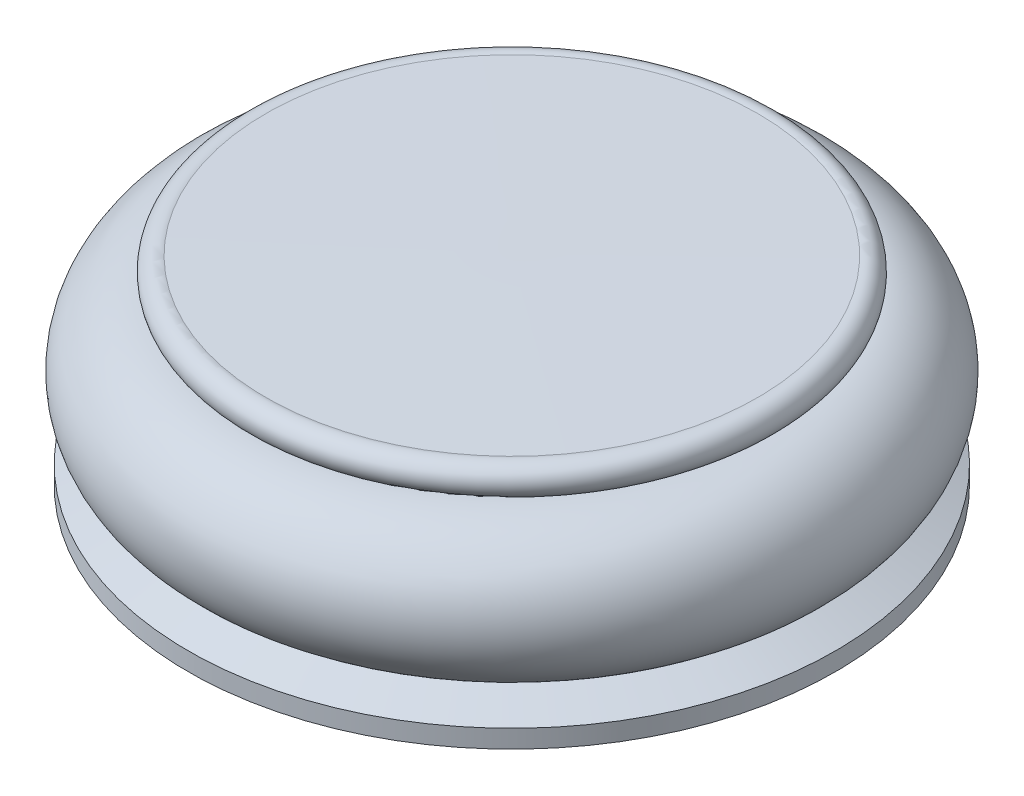
SolidWorks part; units mm, degrees
ref_plane "Front Plane" through (0, 0, 0) normal (0, 0, 1) x (1, 0, 0)
ref_plane "Top Plane" through (0, 0, 0) normal (0, 1, 0) x (1, 0, 0)
ref_plane "Right Plane" through (0, 0, 0) normal (1, 0, 0) x (0, 0, -1)
sketch "Sketch1" plane through (0, 0, 0) normal (0, 0, 1) x (1, 0, 0)
  line L0 (0, -9.6219) -> (0, 0) construction
  line L1 (0, 0) -> (0, -9.6219)
  line L2 (12.247, -1.4324) -> (12.247, -1.4388)
  line L3 (0, -9.6219) -> (15.5627, -9.6219)
  line L4 (15.5627, -9.6219) -> (15.5627, -8.7515)
  line L5 (15.5627, -8.7515) -> (13.8939, -7.9606)
  line L6 (11.827, -0.0671) -> (0, 0)
  arc A0 (11.827, -0.0671) -> (12.247, -1.4324) centre (12.0227, -0.7542) cw
  arc A1 (13.8939, -7.9606) -> (12.247, -1.4388) centre (12.4226, -4.8633) ccw
  dimension "D1" = 0.0064
  dimension "D4" = 0.7144
  dimension "D3" = 3.429
revolve "Revolve1" add sketch "Sketch1" angle 360 about L0
